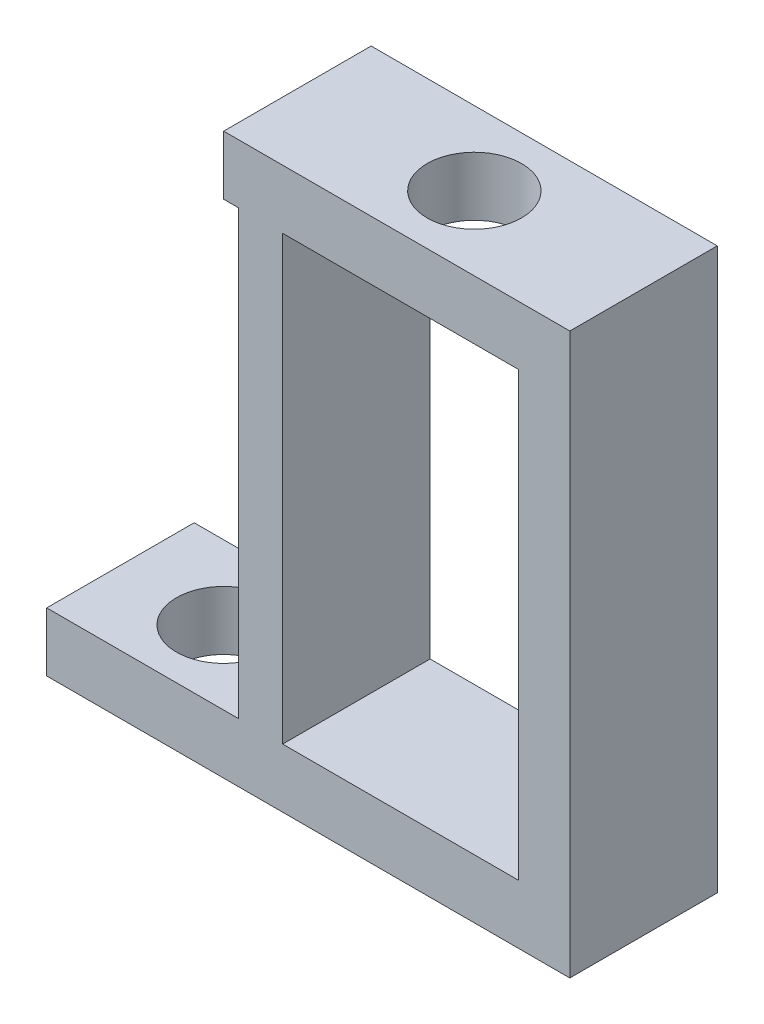
SolidWorks part; units mm, degrees
ref_plane "Front Plane" through (0, 0, 0) normal (0, 0, 1) x (1, 0, 0)
ref_plane "Top Plane" through (0, 0, 0) normal (0, 1, 0) x (1, 0, 0)
ref_plane "Right Plane" through (0, 0, 0) normal (1, 0, 0) x (0, 0, -1)
sketch "Sketch1" plane through (0, 0, 0) normal (0, 1, 0) x (1, 0, 0)
  line L1 (-7, 3) -> (3, 3)
  line L2 (-7, 3) -> (-7, -2)
  line L3 (-7, -2) -> (3, -2)
  line L4 (3, 3) -> (3, -2)
  circle A0 centre (-1, 0.5) radius 1.6
  dimension "D6" = 3.2
  dimension "D1" = 10
  dimension "D2" = 5
  dimension "D3" = 4
  dimension "D4" = 2.5
extrude "Boss-Extrude2" add sketch "Sketch1" along normal blind 2
sketch "Sketch2" plane through (0, 0, 0) normal (0, -1, 0) x (1, 0, 0)
  line L0 (3, -3) -> (-7, -3) construction
  line L1 (-6.5, 2) -> (-5, 2)
  line L2 (-6.5, 2) -> (-6.5, -3)
  line L3 (-6.5, -3) -> (-5, -3)
  line L4 (-5, 2) -> (-5, -3)
  line L5 (-7, -3) -> (-7, 2) construction
  dimension "D1" = 1.5
  dimension "D2" = 0.5
extrude "Boss-Extrude3" add sketch "Sketch2" along normal blind 15
sketch "Sketch3" plane through (0, -15, 0) normal (0, -1, 0) x (1, 0, 0)
  line L0 (-6.5, -3) -> (-5, -3) construction
  line L1 (-5, 2) -> (-13, 2)
  line L2 (-5, 2) -> (-5, -3)
  line L3 (-5, -3) -> (-13, -3)
  line L4 (-13, 2) -> (-13, -3)
  circle A0 centre (-9.5, -0.5) radius 1.6
  circle A1 centre (-1, -0.5) radius 1.6 construction
  dimension "D2" = 3.2
  dimension "D3" = 8.5
  dimension "D1" = 0
  dimension "D4" = 8
  dimension "D5" = 2.5
extrude "Boss-Extrude4" add sketch "Sketch3" along normal blind 2
sketch "Sketch4" plane through (0, 0, 2) normal (0, 0, 1) x (1, 0, 0)
  line L0 (4.7377, -17) -> (4.7377, 2)
  line L1 (-5, -17) -> (4.7377, -17)
  line L2 (-5, -17) -> (-13, -17) construction
  line L3 (4.7377, 2) -> (3, 2)
  line L4 (3, 2) -> (3, -15)
  line L5 (3, -15) -> (-5, -15)
  line L7 (-5, -17) -> (-5, 0) construction
  line L8 (-5, -15) -> (-5, -17)
extrude "Boss-Extrude5" add sketch "Sketch4" against normal up to vertex (5 mm away)
